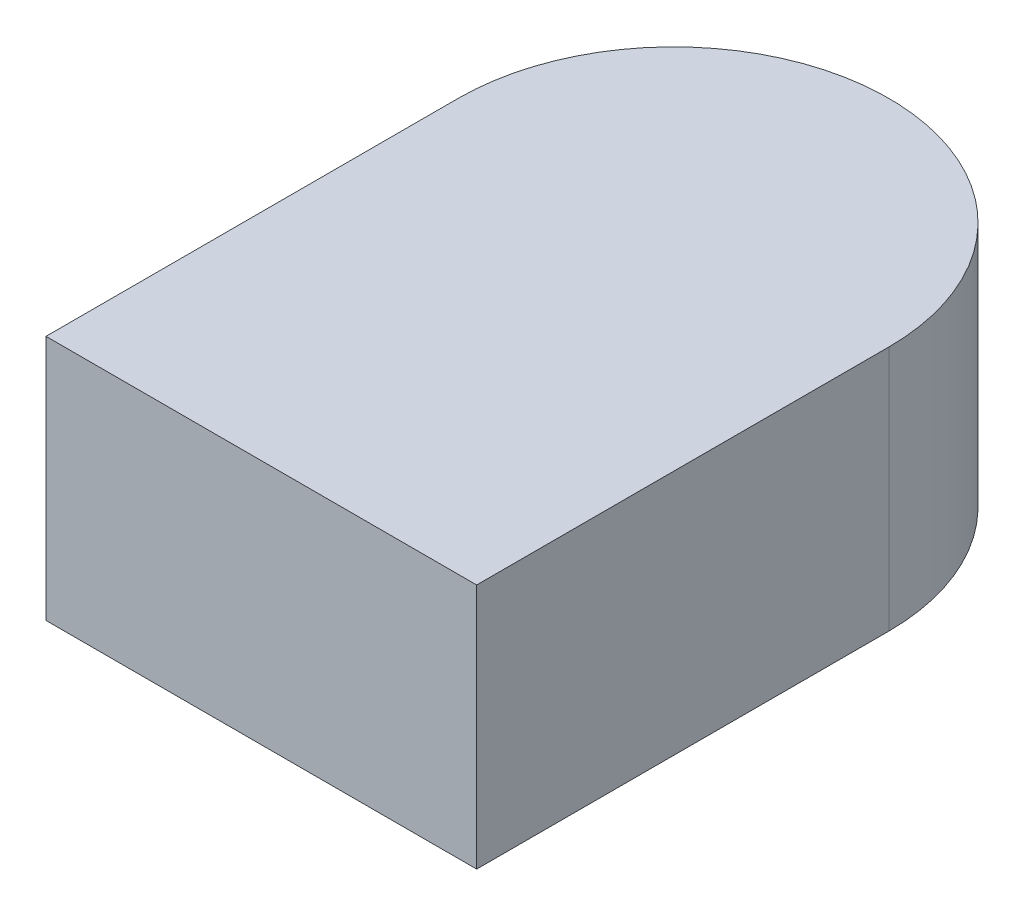
SolidWorks part; units mm, degrees
ref_plane "Front Plane" through (0, 0, 0) normal (0, 0, 1) x (1, 0, 0)
ref_plane "Top Plane" through (0, 0, 0) normal (0, 1, 0) x (1, 0, 0)
ref_plane "Right Plane" through (0, 0, 0) normal (1, 0, 0) x (0, 0, -1)
sketch "Sketch1" plane through (0, 0, 0) normal (0, 1, 0) x (1, 0, 0)
  line L1 (-0.175, 0.1675) -> (0.175, 0.1675) construction
  line L2 (-0.175, 0.1675) -> (-0.175, -0.1675)
  line L3 (-0.175, -0.1675) -> (0.175, -0.1675)
  line L4 (0.175, 0.1675) -> (0.175, -0.1675)
  line L5 (-0.175, 0.1675) -> (0.175, -0.1675) construction
  line L6 (-0.175, -0.1675) -> (0.175, 0.1675) construction
  arc A0 (0.175, 0.1675) -> (-0.175, 0.1675) centre (0, 0.1675) ccw
  point P0 (0, 0)
  point P7 (0, 0.3425)
  dimension "D1" = 0.35
  dimension "D2" = 0.51
extrude "Boss-Extrude1" add sketch "Sketch1" along normal blind 0.2
